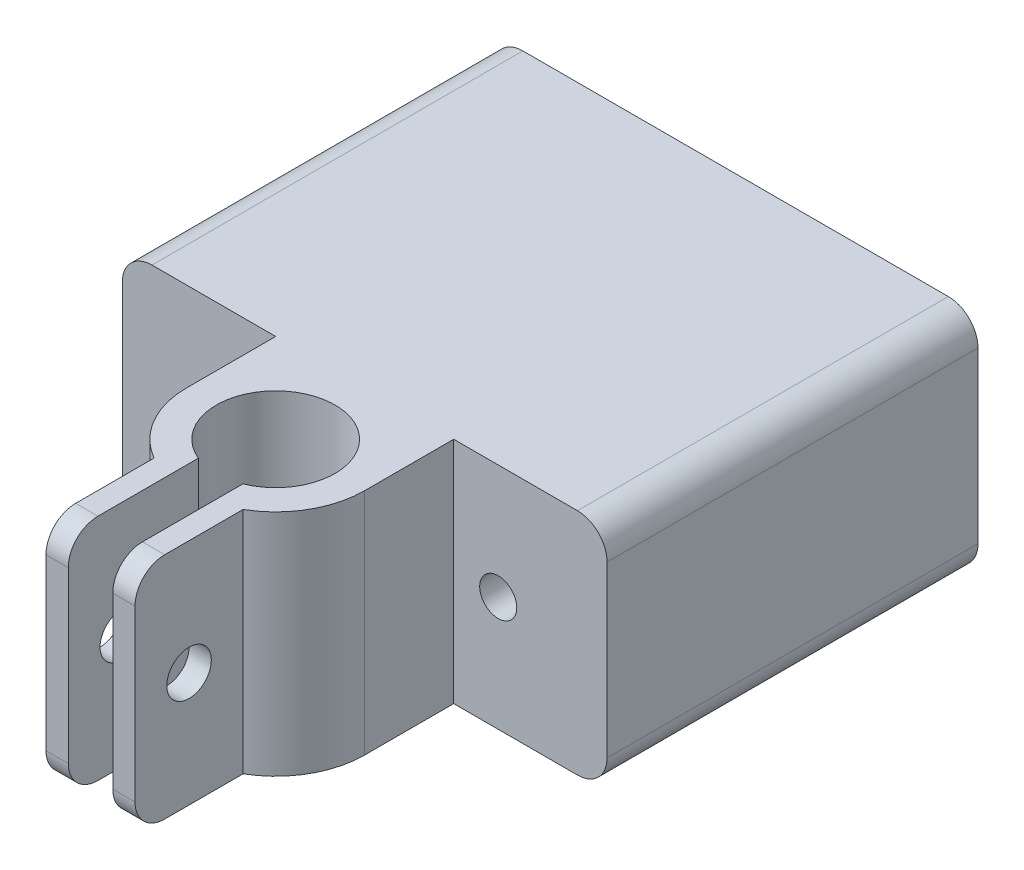
SolidWorks part; units mm, degrees
ref_plane "前视基准面" through (0, 0, 0) normal (0, 0, 1) x (1, 0, 0)
ref_plane "上视基准面" through (0, 0, 0) normal (0, 1, 0) x (1, 0, 0)
ref_plane "右视基准面" through (0, 0, 0) normal (1, 0, 0) x (0, 0, -1)
sketch "草图1" plane through (0, 0, 0) normal (0, 0, 1) x (1, 0, 0)
  line L0 (12.612, 26.3586) -> (-20.0654, 26.3586) construction
  line L2 (-20.0654, 34.0751) -> (12.612, 34.0751)
  line L3 (-20.0654, 34.0751) -> (-20.0654, 18.6421)
  line L4 (-20.0654, 18.6421) -> (12.612, 18.6421)
  line L5 (12.612, 34.0751) -> (12.612, 18.6421)
  line L6 (-20.0654, 34.0751) -> (12.612, 18.6421) construction
  line L7 (-20.0654, 18.6421) -> (12.612, 34.0751) construction
  point P4 (-3.7267, 26.3586)
extrude "凸台-拉伸1" add sketch "草图1" against normal blind 25
sketch "草图2" plane through (0, 0, 0) normal (0, 0, 1) x (1, 0, 0)
  line L0 (-3.7267, 34.0751) -> (-3.7267, 18.6421) construction
  line L3 (12.612, 34.0751) -> (-20.0654, 34.0751) construction
  line L4 (-20.0654, 18.6421) -> (12.612, 18.6421) construction
  line L5 (-3.7267, 26.3586) -> (5.2733, 26.3586) construction
  line L6 (-3.7267, 26.3586) -> (-12.7267, 26.3586) construction
  circle A2 centre (-12.7267, 26.3586) radius 1.25
  circle A3 centre (5.2733, 26.3586) radius 1.25
extrude "切除-拉伸1" cut sketch "草图2" against normal through all
sketch "草图3" plane through (0, 18.6421, 0) normal (0, -1, 0) x (1, 0, 0)
  line L0 (-20.0654, 0) -> (12.612, 0) construction
  line L1 (-3.7267, 0) -> (-3.7267, 6) construction
  circle A0 centre (-3.7267, 6) radius 6
  point P0 (-3.7267, 0)
extrude "凸台-拉伸2" add sketch "草图3" against normal up to surface (15.433 mm away) separate body up to face at (-3.7267, 34.0751, -12.5)
sketch "草图4" plane through (0, 18.6421, 0) normal (0, -1, 0) x (1, 0, 0)
  circle A0 centre (-3.7267, 6) radius 4
extrude "切除-拉伸2" cut sketch "草图4" against normal through all
sketch "草图5" plane through (0, 18.6421, 0) normal (0, -1, 0) x (1, 0, 0)
  line L0 (-9.7267, 6) -> (-9.7267, 0)
  line L1 (-20.0654, 0) -> (12.612, 0) construction
  line L2 (-9.7267, 0) -> (-3.7267, 0)
  line L3 (-3.7267, 0) -> (-9.7267, 6)
  line L4 (-3.7267, 0) -> (2.2733, 6)
  line L5 (2.2733, 6) -> (2.2733, 0)
  line L6 (2.2733, 0) -> (-3.7267, 0)
  circle A0 centre (-3.7267, 6) radius 6 construction
extrude "凸台-拉伸3" add sketch "草图5" against normal up to surface (15.433 mm away) contours L3 L0 L2 | L4 L5 L6 up to face at (-3.7267, 34.0751, 2)
sketch "草图6" plane through (0, 18.6421, 0) normal (0, -1, 0) x (1, 0, 0)
  line L0 (-3.7267, 10) -> (2.2733, 10) construction
  line L2 (-0.7267, 10) -> (-6.7267, 10)
  line L3 (-0.7267, 10) -> (-0.7267, 18.4812)
  line L4 (-0.7267, 18.4812) -> (-6.7267, 18.4812)
  line L5 (-6.7267, 10) -> (-6.7267, 18.4812)
  circle A0 centre (-3.7267, 6) radius 4 construction
extrude "凸台-拉伸4" add sketch "草图6" against normal up to surface (15.433 mm away) up to face at (-3.7267, 34.0751, -4)
sketch "草图8" plane through (0, 18.6421, 0) normal (0, -1, 0) x (1, 0, 0)
  line L0 (0.2733, 6) -> (-7.7267, 6) construction
  line L2 (-2.2267, 6) -> (-5.2267, 6)
  line L3 (-2.2267, 6) -> (-2.2267, 31.3784)
  line L4 (-2.2267, 31.3784) -> (-5.2267, 31.3784)
  line L5 (-5.2267, 6) -> (-5.2267, 31.3784)
  circle A1 centre (-3.7267, 6) radius 4 construction
  point P8 (-3.7267, 6)
  point P9 (-3.7267, 6)
extrude "切除-拉伸5" cut sketch "草图8" against normal through all
sketch "草图9" plane through (-0.7267, 0, 0) normal (1, 0, 0) x (0, 0, -1)
  line L0 (-14.8387, 34.0751) -> (-14.8387, 24.9373) construction
  line L1 (-11.1962, 34.0751) -> (-18.4812, 34.0751) construction
  line L2 (-18.4812, 26.3586) -> (-11.1962, 26.3586) construction
  line L3 (-18.4812, 34.0751) -> (-18.4812, 18.6421) construction
  line L4 (-11.1962, 18.6421) -> (-11.1962, 34.0751) construction
  circle A0 centre (-14.8387, 26.3586) radius 1.5
extrude "切除-拉伸6" cut sketch "草图9" against normal through all
fillet "圆角1" radius 2 4 edges at (12.612, 18.6421, -12.5) (12.612, 34.0751, -12.5) (-20.0654, 18.6421, -12.5) (-20.0654, 34.0751, -12.5)
fillet "圆角2" radius 2 4 edges at (-5.9767, 34.0751, 18.4812) (-5.9767, 18.6421, 18.4812) (-1.4767, 18.6421, 18.4812) (-1.4767, 34.0751, 18.4812)
